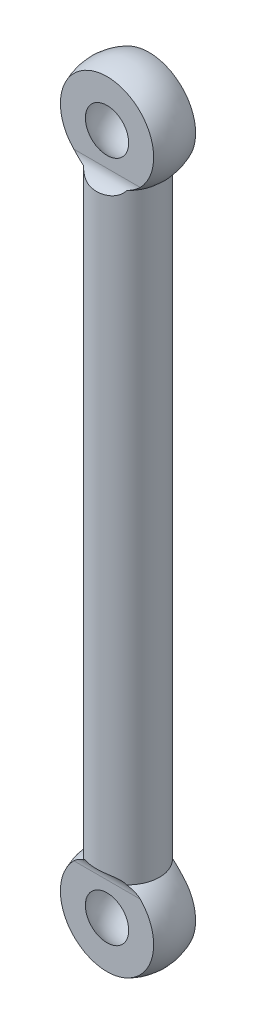
SolidWorks part; units mm, degrees
ref_plane "Front Plane" through (0, 0, 0) normal (0, 0, 1) x (1, 0, 0)
ref_plane "Top Plane" through (0, 0, 0) normal (0, 1, 0) x (1, 0, 0)
ref_plane "Right Plane" through (0, 0, 0) normal (1, 0, 0) x (0, 0, -1)
sketch "Sketch1" plane through (0, 0, 0) normal (0, 1, 0) x (1, 0, 0)
  circle A0 centre (0, 0) radius 3.048
  dimension "D1" = 6.096
extrude "Boss-Extrude1" add sketch "Sketch1" along normal blind 33.02
sketch "Sketch2" plane through (0, 0, 0) normal (0, 0, 1) x (1, 0, 0)
  line L1 (-3.048, 33.02) -> (3.048, 33.02) construction
  line L2 (0, 37.973) -> (0, 35.941)
  line L3 (0, 30.099) -> (0, 28.067)
  arc A0 (0, 37.973) -> (0, 28.067) centre (0, 33.02) ccw
  arc A1 (0, 35.941) -> (0, 30.099) centre (0, 33.02) ccw
  dimension "D1" = 9.906
  dimension "D2" = 5.842
revolve "Revolve3" add sketch "Sketch2" angle 360 about L2
sketch "Sketch3" plane through (0, 0, 0) normal (1, 0, 0) x (0, 0, -1)
  line L0 (2.032, 37.973) -> (-2.032, 37.973) construction
  line L1 (-2.032, 37.973) -> (-2.032, 29.845)
  line L2 (-3.556, 28.321) -> (-6.35, 28.321)
  line L3 (6.35, 37.973) -> (2.032, 37.973)
  line L4 (-6.35, 28.321) -> (-6.35, 37.973)
  line L5 (-2.032, 37.973) -> (-6.35, 37.973)
  line L6 (6.35, 37.973) -> (6.35, 28.321)
  line L7 (6.35, 28.321) -> (3.556, 28.321)
  line L8 (2.032, 29.845) -> (2.032, 37.973)
  arc A0 (-2.032, 29.845) -> (-3.556, 28.321) centre (-3.556, 29.845) cw
  arc A1 (2.032, 29.845) -> (3.556, 28.321) centre (3.556, 29.845) ccw
  point P5 (0, 37.973)
  dimension "D2" = 1.524
  dimension "D1" = 12.7
  dimension "D3" = 4.064
  dimension "D4" = 9.652
extrude "Cut-Extrude1" cut sketch "Sketch3" against normal through all both and the other way through all
sketch "Sketch4" plane through (0, 0, 0) normal (0, 0, 1) x (1, 0, 0)
  line L0 (0, 35.941) -> (0, 30.099)
  arc A0 (0, 30.099) -> (0, 35.941) centre (0, 33.02) cw
  arc A1 (0, 35.941) -> (0, 30.099) centre (0, 33.02) ccw construction
revolve "Cut-Revolve1" cut sketch "Sketch4" angle 360 about L0
mirror "Mirror1" about plane through (0, 0, 0) normal (0, 1, 0) of bodies 104
